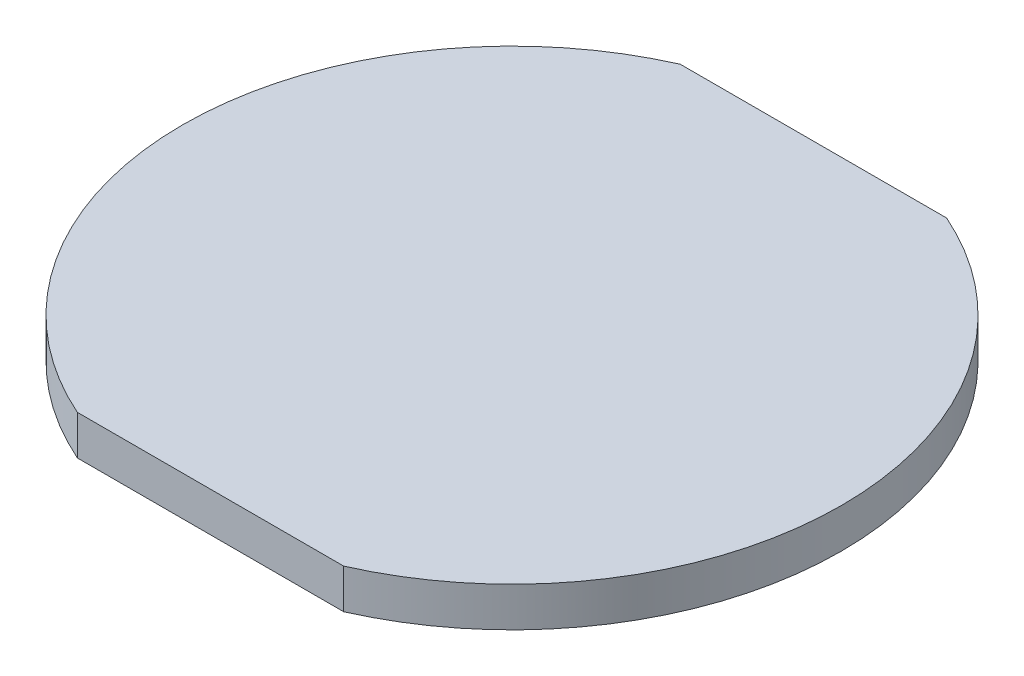
SolidWorks part; units mm, degrees
ref_plane "Front Plane" through (0, 0, 0) normal (0, 0, 1) x (1, 0, 0)
ref_plane "Top Plane" through (0, 0, 0) normal (0, 1, 0) x (1, 0, 0)
ref_plane "Right Plane" through (0, 0, 0) normal (1, 0, 0) x (0, 0, -1)
sketch "Sketch1" plane through (0, 0, 0) normal (0, 1, 0) x (1, 0, 0)
  line L0 (0, 25) -> (0, -25) construction
  line L1 (-25, 0) -> (25, 0) construction
  line L2 (10.1, -22.869) -> (-10.1, -22.869)
  line L3 (10.1, 22.869) -> (-10.1, 22.869)
  arc A0 (-10.1, 22.869) -> (-10.1, -22.869) centre (0, 0) ccw
  arc A1 (10.1, -22.869) -> (10.1, 22.869) centre (0, 0) ccw
  dimension "D1" = 50
  dimension "D2" = 20.2
extrude "Boss-Extrude1" add sketch "Sketch1" along normal blind 3
